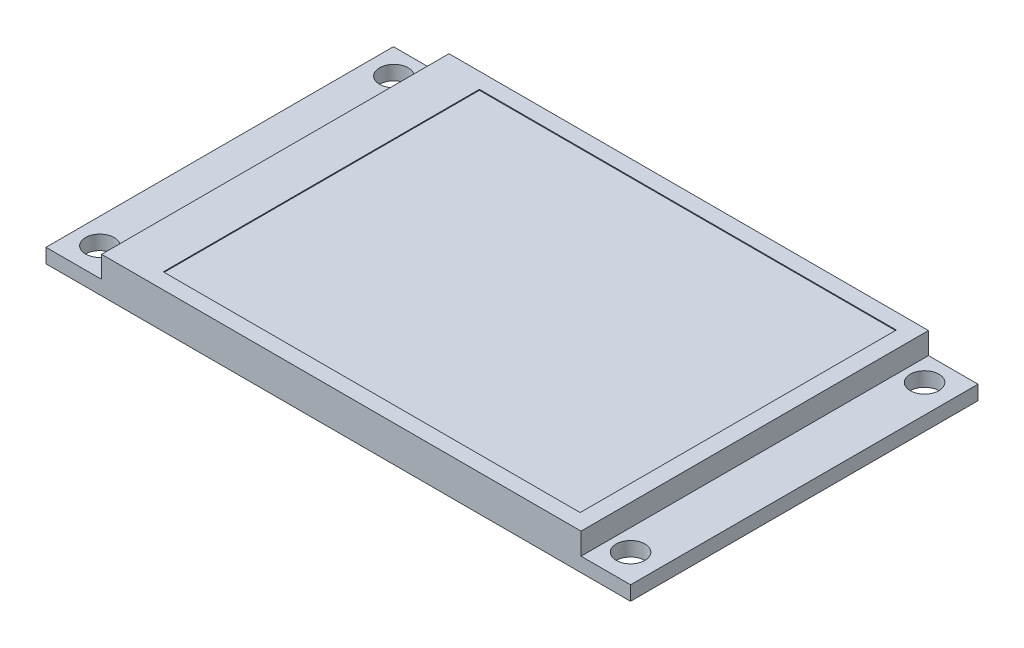
SolidWorks part; units mm, degrees
ref_plane "Front Plane" through (0, 0, 0) normal (0, 0, 1) x (1, 0, 0)
ref_plane "Top Plane" through (0, 0, 0) normal (0, 1, 0) x (1, 0, 0)
ref_plane "Right Plane" through (0, 0, 0) normal (1, 0, 0) x (0, 0, -1)
sketch "Sketch1" plane through (0, 0, 0) normal (0, 1, 0) x (1, 0, 0)
  line L0 (-32.35, 8.0373) -> (-32.35, 18.75) construction
  line L1 (-33.65, -20) -> (33.65, -20)
  line L2 (-33.65, -20) -> (-33.65, 20)
  line L3 (-33.65, 20) -> (33.65, 20)
  line L4 (33.65, -20) -> (33.65, 20)
  line L5 (-33.65, -20) -> (33.65, 20) construction
  line L6 (-33.65, 20) -> (33.65, -20) construction
  line L7 (-30.7, 17.1) -> (30.4, 17.1) construction
  line L8 (-30.7, 17.1) -> (-30.7, -16.75) construction
  line L9 (-30.7, -16.75) -> (30.4, -16.75) construction
  line L10 (30.4, 17.1) -> (30.4, -16.75) construction
  line L11 (-32.35, 18.75) -> (-21.6373, 18.75) construction
  line L12 (32.05, -7.6873) -> (32.05, -18.4) construction
  line L13 (32.05, -18.4) -> (21.3373, -18.4) construction
  circle A0 centre (-30.7, 17.1) radius 1.65
  circle A1 centre (-30.7, -16.75) radius 1.65
  circle A2 centre (30.4, -16.75) radius 1.65
  circle A3 centre (30.4, 17.1) radius 1.65
  point P0 (0, 0)
  dimension "D3" = 3.3
  dimension "D6" = 1.25
  dimension "D1" = 40
  dimension "D2" = 67.3
  dimension "D4" = 1.3
  dimension "D5" = 1.6
  dimension "D7" = 1.6
extrude "Boss-Extrude1" add sketch "Sketch1" along normal blind 1.65
sketch "Sketch2" plane through (0, 1.65, 0) normal (0, 1, 0) x (1, 0, 0)
  line L0 (33.65, 20) -> (-33.65, 20) construction
  line L1 (-27.25, -20) -> (27.95, -20)
  line L2 (-27.25, -20) -> (-27.25, 20)
  line L3 (-27.25, 20) -> (27.95, 20)
  line L4 (27.95, -20) -> (27.95, 20)
  line L5 (-33.65, -20) -> (33.65, -20) construction
  line L6 (-33.65, 20) -> (-33.65, -20) construction
  line L7 (33.65, -20) -> (33.65, 20) construction
  dimension "D1" = 6.4
  dimension "D2" = 5.7
extrude "Boss-Extrude2" add sketch "Sketch2" along normal blind 2.5
sketch "Sketch3" plane through (0, 4.15, 0) normal (0, 1, 0) x (1, 0, 0)
  line L0 (-33.65, 20) -> (-33.65, -20) construction
  line L1 (-21.95, 18.2) -> (26.05, 18.2)
  line L2 (-21.95, 18.2) -> (-21.95, -18.2)
  line L3 (-21.95, -18.2) -> (26.05, -18.2)
  line L4 (26.05, 18.2) -> (26.05, -18.2)
  line L5 (27.95, 20) -> (-27.25, 20) construction
  line L6 (-27.25, -20) -> (27.95, -20) construction
  line L7 (33.65, -20) -> (33.65, 20) construction
  dimension "D1" = 11.7
  dimension "D2" = 1.8
  dimension "D3" = 1.8
  dimension "D4" = 7.6
extrude "Cut-Extrude1" cut sketch "Sketch3" against normal blind 0.1
